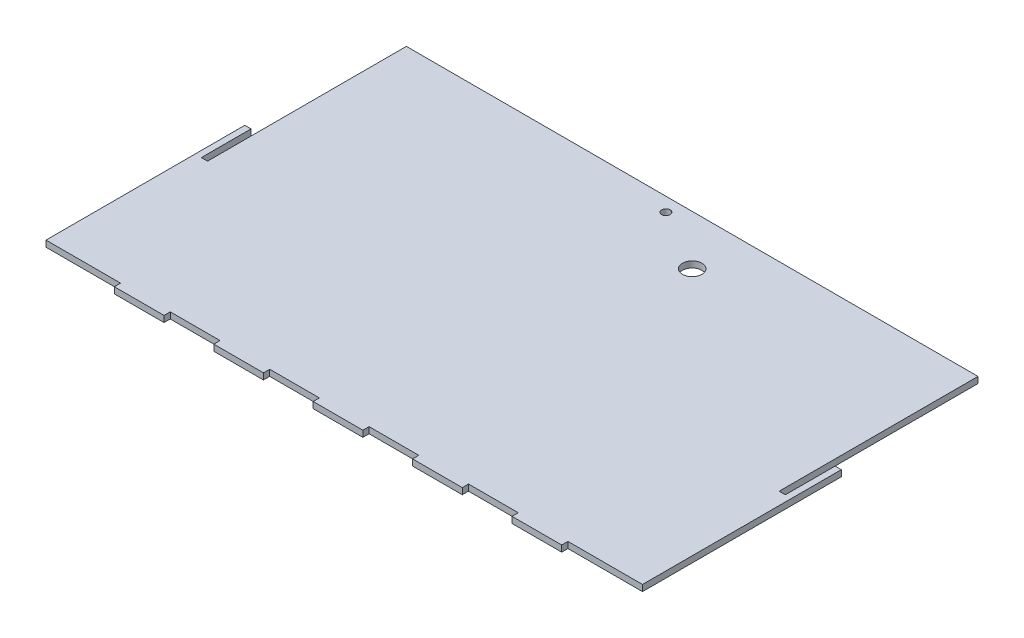
SolidWorks part; units mm, degrees
ref_plane "Front Plane" through (0, 0, 0) normal (0, 0, 1) x (1, 0, 0)
ref_plane "Top Plane" through (0, 0, 0) normal (0, 1, 0) x (1, 0, 0)
ref_plane "Right Plane" through (0, 0, 0) normal (1, 0, 0) x (0, 0, -1)
sketch "Sketch1" plane through (0, 0, 0) normal (0, 1, 0) x (1, 0, 0)
  line L0 (-88.9, -92.075) -> (-63.5, -92.075) construction
  line L1 (-152.4, -88.9) -> (152.4, -88.9)
  line L2 (-152.4, -88.9) -> (-152.4, 88.9)
  line L3 (-152.4, 88.9) -> (152.4, 88.9)
  line L4 (152.4, -88.9) -> (152.4, 88.9)
  line L5 (-152.4, -88.9) -> (152.4, 88.9) construction
  line L6 (-152.4, 88.9) -> (152.4, -88.9) construction
  line L7 (-12.7, -88.9) -> (12.7, -88.9)
  line L8 (-12.7, -88.9) -> (-12.7, -92.075)
  line L9 (-12.7, -92.075) -> (12.7, -92.075)
  line L10 (12.7, -88.9) -> (12.7, -92.075)
  line L11 (38.1, -88.9) -> (63.5, -88.9)
  line L12 (38.1, -88.9) -> (38.1, -92.075)
  line L13 (38.1, -92.075) -> (63.5, -92.075)
  line L14 (63.5, -88.9) -> (63.5, -92.075)
  line L15 (88.9, -88.9) -> (114.3, -88.9)
  line L16 (88.9, -88.9) -> (88.9, -92.075)
  line L17 (88.9, -92.075) -> (114.3, -92.075)
  line L18 (114.3, -88.9) -> (114.3, -92.075)
  line L19 (-63.5, -88.9) -> (-38.1, -88.9)
  line L20 (-63.5, -88.9) -> (-63.5, -92.075)
  line L21 (-63.5, -92.075) -> (-38.1, -92.075)
  line L22 (-38.1, -88.9) -> (-38.1, -92.075)
  line L23 (-114.3, -88.9) -> (-88.9, -88.9)
  line L24 (-114.3, -88.9) -> (-114.3, -92.075)
  line L25 (-114.3, -92.075) -> (-88.9, -92.075)
  line L26 (-88.9, -88.9) -> (-88.9, -92.075)
  line L27 (-38.1, -92.075) -> (-12.7, -92.075) construction
  line L28 (12.7, -92.075) -> (38.1, -92.075) construction
  line L29 (63.5, -92.075) -> (88.9, -92.075) construction
  line L30 (-146.05, 88.9) -> (-146.05, -12.7)
  line L31 (-146.05, -12.7) -> (-149.225, -12.7)
  line L32 (-149.225, -12.7) -> (-149.225, 12.7)
  line L33 (-149.225, 12.7) -> (-152.4, 12.7)
  line L34 (146.05, 88.9) -> (146.05, -12.7)
  line L35 (146.05, -12.7) -> (149.225, -12.7)
  line L36 (149.225, -12.7) -> (149.225, 12.7)
  line L37 (149.225, 12.7) -> (152.4, 12.7)
  circle A0 centre (25.4, 63.5) radius 4.953
  circle A1 centre (-6.35, 81.8322) radius 2.15
  point P0 (0, 0)
  point P32 (0, -92.075)
  dimension "D3" = 4.3
  dimension "D4" = 9.906
  dimension "D1" = 177.8
  dimension "D2" = 304.8
  dimension "D5" = 127
  dimension "D6" = 31.75
  dimension "D7" = 25.4
  dimension "D8" = 18.3322
  dimension "D9" = 25.4
  dimension "D10" = 3.175
  dimension "D11" = 76.2
  dimension "D12" = 25.4
  dimension "D13" = 3.175
extrude "Boss-Extrude1" add sketch "Sketch1" along normal mid plane 3.175
